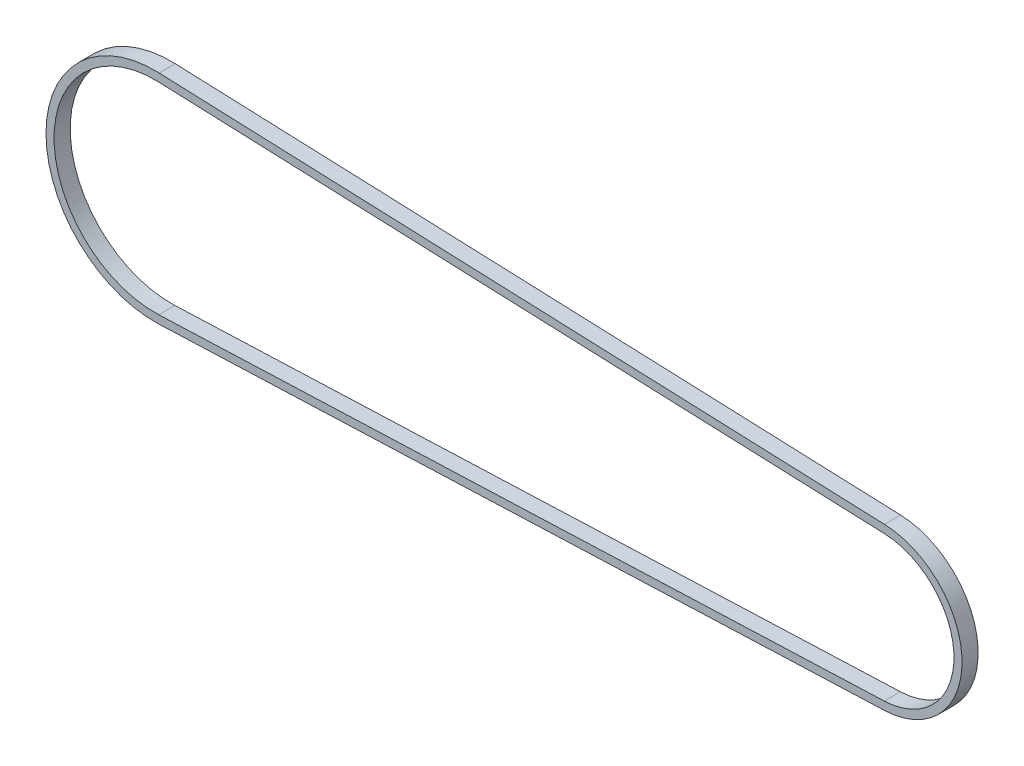
SolidWorks part; units mm, degrees
ref_plane "Front Plane" through (0, 0, 0) normal (0, 0, 1) x (1, 0, 0)
ref_plane "Top Plane" through (0, 0, 0) normal (0, 1, 0) x (1, 0, 0)
ref_plane "Right Plane" through (0, 0, 0) normal (1, 0, 0) x (0, 0, -1)
sketch "Sketch1" plane through (0, 0, 0) normal (0, 0, 1) x (1, 0, 0)
  line L0 (-450, 62.5) -> (0, 45)
  line L1 (-450, -62.5) -> (0, -45)
  arc A0 (-450, 62.5) -> (-450, -62.5) centre (-452.4306, 0) ccw
  arc A1 (0, 45) -> (0, -45) centre (-1.75, 0) cw
extrude "Extrude-Thin2" add sketch "Sketch1" along normal blind 10 thin thin type one direction wall 5
